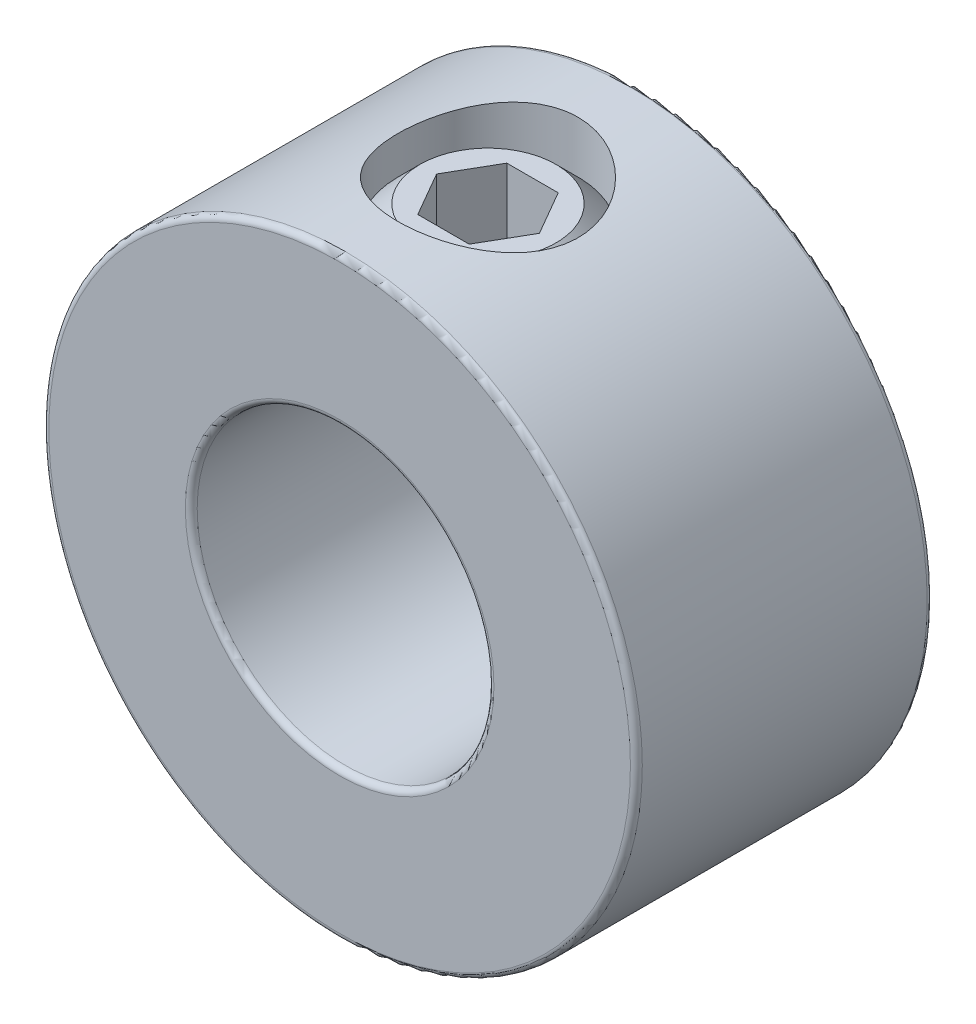
SolidWorks part; units mm, degrees
ref_plane "Front Plane" through (0, 0, 0) normal (0, 0, 1) x (1, 0, 0)
ref_plane "Top Plane" through (0, 0, 0) normal (0, 1, 0) x (1, 0, 0)
ref_plane "Right Plane" through (0, 0, 0) normal (1, 0, 0) x (0, 0, -1)
sketch "Sketch1" plane through (0, 0, 0) normal (0, 0, 1) x (1, 0, 0)
  circle A0 centre (0, 0) radius 7.9375
  circle A1 centre (0, 0) radius 3.9688
  point P4 (7.9375, 0)
  dimension "Bore Dia" = 7.9375
  dimension "OD" = 15.875
extrude "Extrude1" add sketch "Sketch1" along normal mid plane 7.9375
sketch "Sketch2" plane through (41.275, 0, 0) normal (0, -1, 0) x (0, 0, -1)
  line L0 (3.9688, -41.275) -> (-3.9688, -41.275) construction
  line L1 (-3.9688, -33.3375) -> (-3.9688, -49.2125) construction
  line L2 (3.9688, -49.2125) -> (3.9688, -33.3375) construction
  circle A0 centre (0, -41.275) radius 2.413
  point P7 (0, -43.688)
  dimension "Set Screw Dia" = 4.826
extrude "Cut-Extrude1" cut sketch "Sketch2" against normal through all
fillet "Fillet1" radius 0.1588 4 edges at (3.9688, 0, -3.9688) (3.9688, 0, 3.9688) (7.9375, 0, -3.9688) (7.9375, 0, 3.9688)
sketch "Sketch3" plane through (0, 0, 0) normal (0, 0, 1) x (1, 0, 0)
  line L0 (-1.8198, 3.9688) -> (-0.7119, 3.9688)
  line L1 (0, 4.6806) -> (-0.7119, 3.9688)
  line L2 (0, 4.6806) -> (0, 7.1438)
  line L3 (0, 7.1438) -> (-1.8198, 7.1438)
  line L4 (-2.413, 4.562) -> (-2.413, 6.5505)
  line L5 (0, 3.9688) -> (0, 0) construction
  line L6 (-2.413, 4.562) -> (-2.413, 3.9688) construction
  line L7 (-2.413, 3.9688) -> (-1.8198, 3.9688) construction
  line L8 (-2.413, 6.5505) -> (-2.413, 7.1438) construction
  line L9 (-1.8198, 3.9688) -> (-2.413, 4.562)
  line L10 (-2.413, 6.5505) -> (-1.8198, 7.1438)
  line L11 (-2.413, 7.1438) -> (-1.8198, 7.1438) construction
  line L12 (-0.7119, 3.9688) -> (0, 3.9688) construction
  line L13 (0, 3.9688) -> (0, 4.6806) construction
  circle A1 centre (0, 0) radius 3.9688 construction
  dimension "Screw Length" = 3.175
  dimension "D2" = 0.5932
  dimension "D1" = 0.7119
revolve "Revolve1" add sketch "Sketch3" angle 360 about L5
sketch "Sketch4" plane through (3.3734, 7.1437, 0) normal (0, -1, 0) x (0, 0, -1)
  line L1 (0, -1.9986) -> (-1.1906, -2.686)
  line L2 (-1.1906, -2.686) -> (-1.1906, -4.0608)
  line L3 (-1.1906, -4.0608) -> (0, -4.7483)
  line L4 (0, -4.7483) -> (1.1906, -4.0608)
  line L5 (1.1906, -4.0608) -> (1.1906, -2.686)
  line L6 (1.1906, -2.686) -> (0, -1.9986)
  circle A0 centre (0, -3.3734) radius 1.1906 construction
  circle A1 centre (0, -3.3734) radius 1.3748 construction
  dimension "D1" = 2.7496
  dimension "Hex Size" = 2.3813
extrude "Cut-Extrude2" cut sketch "Sketch4" along normal blind 2.3813
equation "\"D1@Fillet1\" = \"OD@Sketch1\"*.01"
equation "\"D1@Cut-Extrude2\" = \"Hex Size@Sketch4\""
equation "\"D2@Sketch3\" =(\"Set Screw Dia@Sketch2\"-\"D1@Sketch4\")/3.5"
equation "\"D1@Sketch3\" = \"D2@Sketch3\"*1.2"
